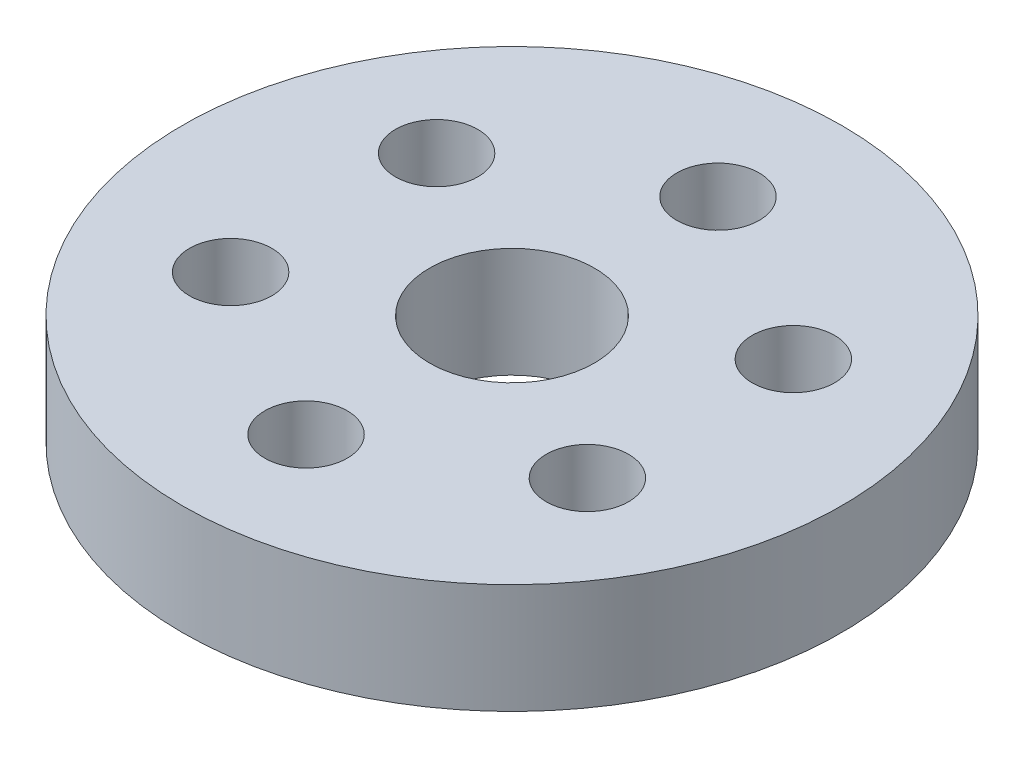
SolidWorks part; units mm, degrees
material "Balsa"
ref_plane "Front Plane" through (0, 0, 0) normal (0, 0, 1) x (1, 0, 0)
ref_plane "Top Plane" through (0, 0, 0) normal (0, 1, 0) x (1, 0, 0)
ref_plane "Right Plane" through (0, 0, 0) normal (1, 0, 0) x (0, 0, -1)
sketch "Sketch1" plane through (0, 0, 0) normal (0, 1, 0) x (1, 0, 0)
  circle A0 centre (0, 0) radius 12.7
  circle A1 centre (0, 0) radius 3.175
  dimension "D1" = 25.4
  dimension "D2" = 6.35
extrude "Boss-Extrude1" add sketch "Sketch1" along normal mid plane 4.2333
sketch "Sketch2" plane through (0, 0, 0) normal (0, 1, 0) x (1, 0, 0)
  line L0 (0, 3.175) -> (0, 12.7) construction
  circle A0 centre (0, 7.9375) radius 1.5875
  circle A1 centre (0, 0) radius 3.175 construction
  circle A2 centre (0, 0) radius 12.7 construction
  circle A3 centre (6.8741, 3.9688) radius 1.5875
  circle A4 centre (6.8741, -3.9687) radius 1.5875
  circle A5 centre (0, -7.9375) radius 1.5875
  circle A6 centre (-6.8741, -3.9688) radius 1.5875
  circle A7 centre (-6.8741, 3.9687) radius 1.5875
  point P9 (0, 7.9375)
  point P23 (0, 0)
  dimension "D1" = 3.175
  dimension "D2" = 6
extrude "Cut-Extrude1" cut sketch "Sketch2" against normal through all and the other way through all
